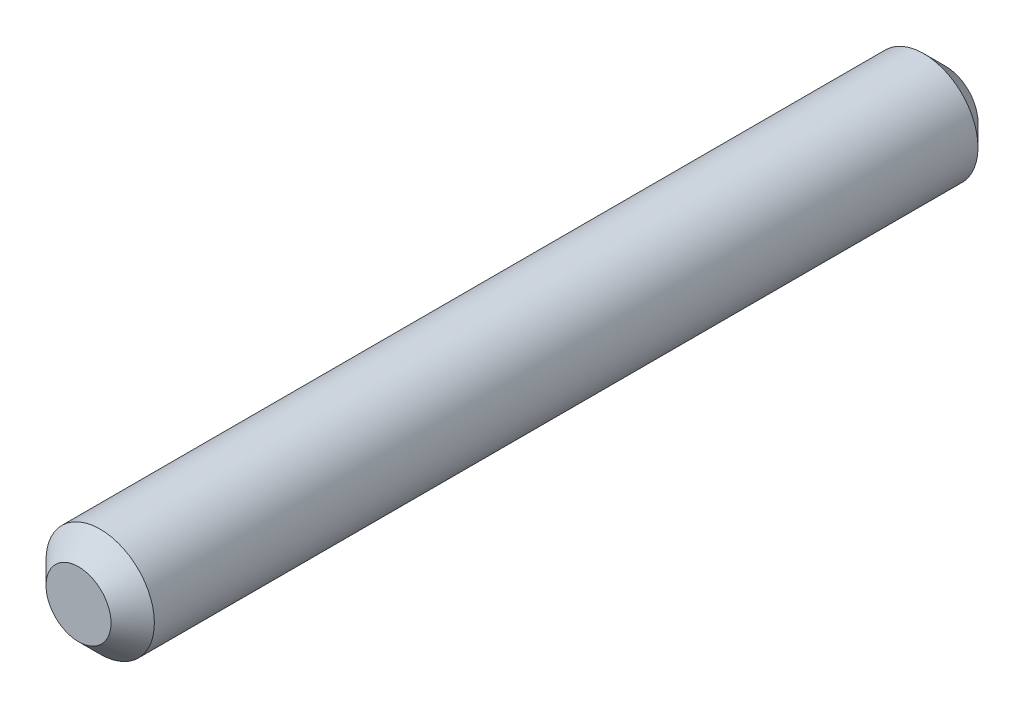
SolidWorks part; units mm, degrees
material "Alloy Steel"
ref_plane "Front Plane" through (0, 0, 0) normal (0, 0, 1) x (1, 0, 0)
ref_plane "Top Plane" through (0, 0, 0) normal (0, 1, 0) x (1, 0, 0)
ref_plane "Right Plane" through (0, 0, 0) normal (1, 0, 0) x (0, 0, -1)
sketch "Sketch3" plane through (0, 0, 0) normal (0, 0, 1) x (1, 0, 0)
  circle A0 centre (0, 0) radius 3.175
  dimension "D1" = 6.35
extrude "Boss-Extrude1" add sketch "Sketch3" along normal blind 50.8
chamfer "Chamfer1" distance 1.27 angle 45 2 edges at (3.175, 0, 0) (3.175, 0, 50.8)
